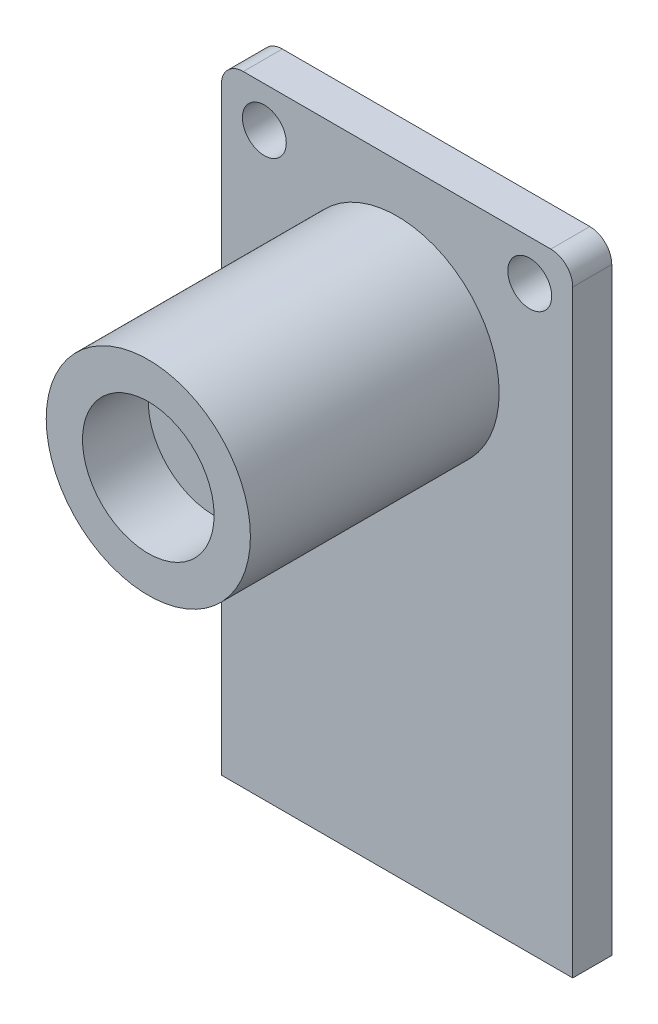
SolidWorks part; units mm, degrees
ref_plane "Front Plane" through (0, 0, 0) normal (0, 0, 1) x (1, 0, 0)
ref_plane "Top Plane" through (0, 0, 0) normal (0, 1, 0) x (1, 0, 0)
ref_plane "Right Plane" through (0, 0, 0) normal (1, 0, 0) x (0, 0, -1)
sketch "Sketch1" plane through (0, 0, 0) normal (0, 0, 1) x (1, 0, 0)
  line L1 (8.01, -14.14) -> (-8.01, -14.14)
  line L2 (8.01, -14.14) -> (8.01, 13.14)
  line L3 (7.01, 14.14) -> (-7.01, 14.14)
  line L4 (-8.01, -14.14) -> (-8.01, 13.14)
  arc A0 (8.01, 13.14) -> (7.01, 14.14) centre (7.01, 13.14) ccw
  arc A1 (-8.01, 13.14) -> (-7.01, 14.14) centre (-7.01, 13.14) cw
  point P0 (0, 0)
  dimension "D1" = 1
extrude "Boss-Extrude1" add sketch "Sketch1" along normal blind 1.78
sketch "Sketch2" plane through (0, 0, 1.78) normal (0, 0, 1) x (1, 0, 0)
  line L0 (7.01, 14.14) -> (-7.01, 14.14) construction
  circle A0 centre (0, 7.285) radius 4.655
  dimension "D1" = 6.855
extrude "Boss-Extrude2" add sketch "Sketch2" along normal blind 11.34
sketch "Sketch3" plane through (0, 0, 13.12) normal (0, 0, 1) x (1, 0, 0)
  circle A0 centre (0, 7.285) radius 3
extrude "Cut-Extrude1" cut sketch "Sketch3" against normal blind 3
sketch "Sketch4" plane through (0, 0, 1.78) normal (0, 0, 1) x (1, 0, 0)
  circle A1 centre (6.05, 12.2999) radius 1
  circle A2 centre (-6.05, 12.2999) radius 1
extrude "Cut-Extrude2" cut sketch "Sketch4" against normal blind 3
